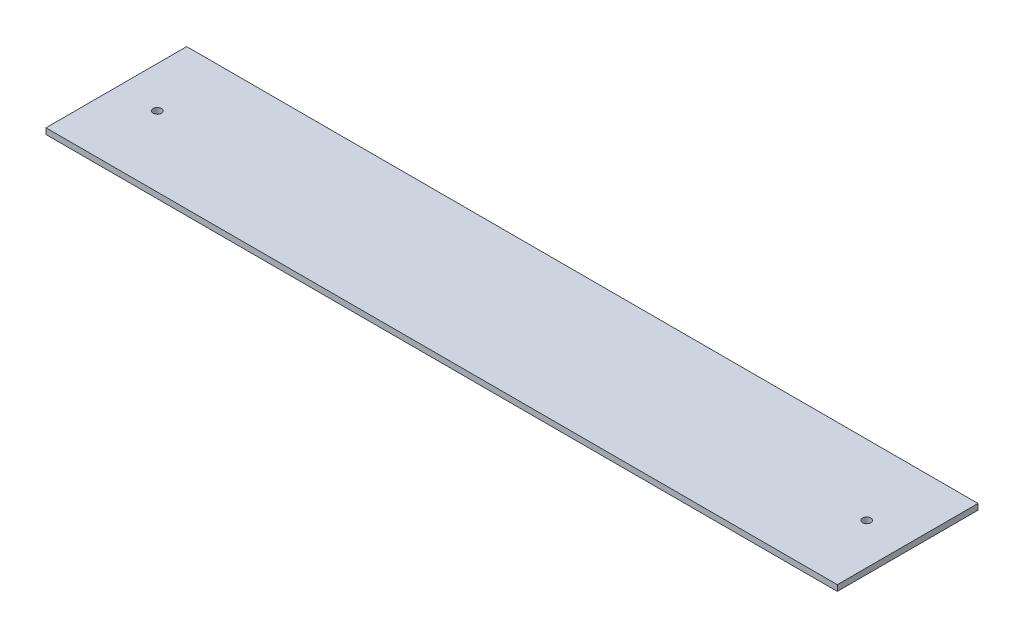
SolidWorks part; units mm, degrees
ref_plane "Front Plane" through (0, 0, 0) normal (0, 0, 1) x (1, 0, 0)
ref_plane "Top Plane" through (0, 0, 0) normal (0, 1, 0) x (1, 0, 0)
ref_plane "Right Plane" through (0, 0, 0) normal (1, 0, 0) x (0, 0, -1)
sketch "Sketch1" plane through (0, 0, 0) normal (0, 1, 0) x (1, 0, 0)
  line L0 (0, 38.1) -> (0, -38.1) construction
  line L1 (214.3125, -38.1) -> (-214.3125, -38.1)
  line L2 (214.3125, -38.1) -> (214.3125, 38.1)
  line L3 (214.3125, 38.1) -> (-214.3125, 38.1)
  line L4 (-214.3125, -38.1) -> (-214.3125, 38.1)
  line L5 (214.3125, -38.1) -> (-214.3125, 38.1) construction
  line L6 (214.3125, 38.1) -> (-214.3125, -38.1) construction
  circle A0 centre (-192.0875, 0) radius 2.25
  circle A1 centre (192.0875, 0) radius 2.25
  point P0 (0, 0)
  dimension "D3" = 4.5
  dimension "D1" = 428.625
  dimension "D2" = 76.2
  dimension "D4" = 22.225
  dimension "D5" = 38.1
extrude "Boss-Extrude1" add sketch "Sketch1" against normal blind 3.175
